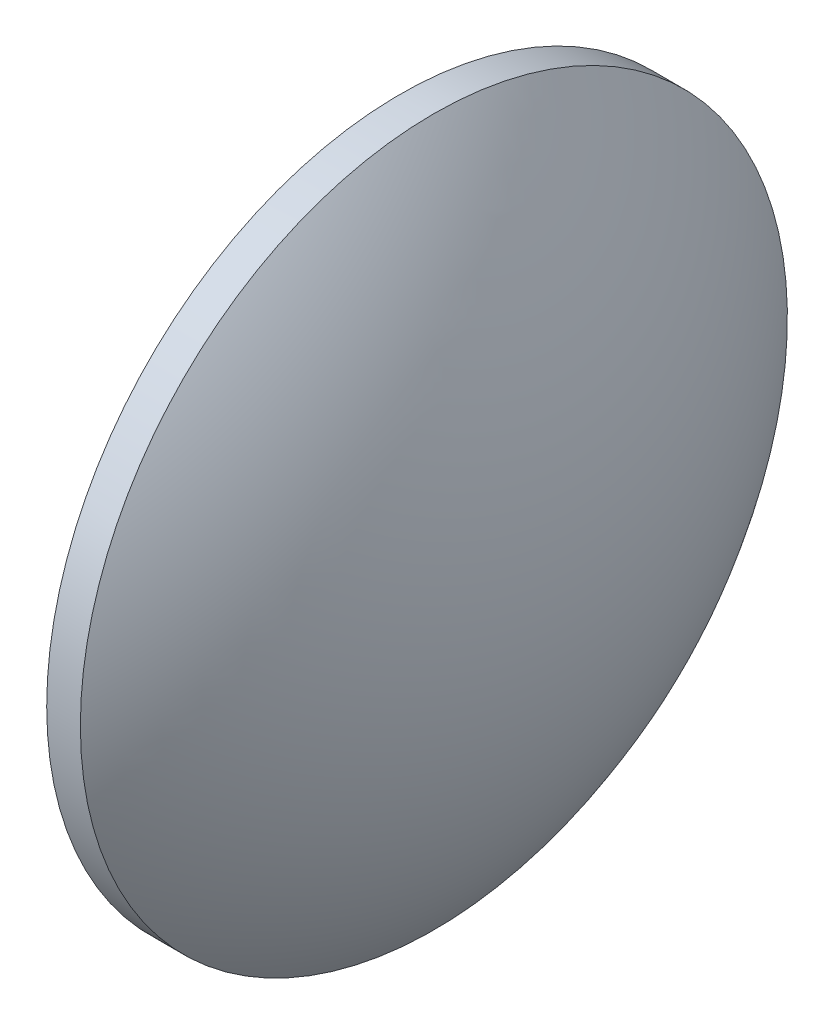
SolidWorks part; units mm, degrees
ref_plane "前视基准面" through (0, 0, 0) normal (0, 0, 1) x (1, 0, 0)
ref_plane "上视基准面" through (0, 0, 0) normal (0, 1, 0) x (1, 0, 0)
ref_plane "右视基准面" through (0, 0, 0) normal (1, 0, 0) x (0, 0, -1)
sketch "草图1" plane through (0, 0, 0) normal (0, 0, 1) x (1, 0, 0)
  line L0 (366.6622, 17.7317) -> (420.4452, 17.7317) construction
  line L1 (385.7011, 17.7317) -> (385.7011, 49.2317)
  line L2 (399.4211, 17.7317) -> (385.7011, 17.7317)
  line L3 (385.7011, 49.2317) -> (388.7011, 49.2317)
  arc A0 (399.4211, 17.7317) -> (388.7011, 49.2317) centre (347.7808, 17.7317) ccw
revolve "旋转1" add sketch "草图1" angle 360 about L0
